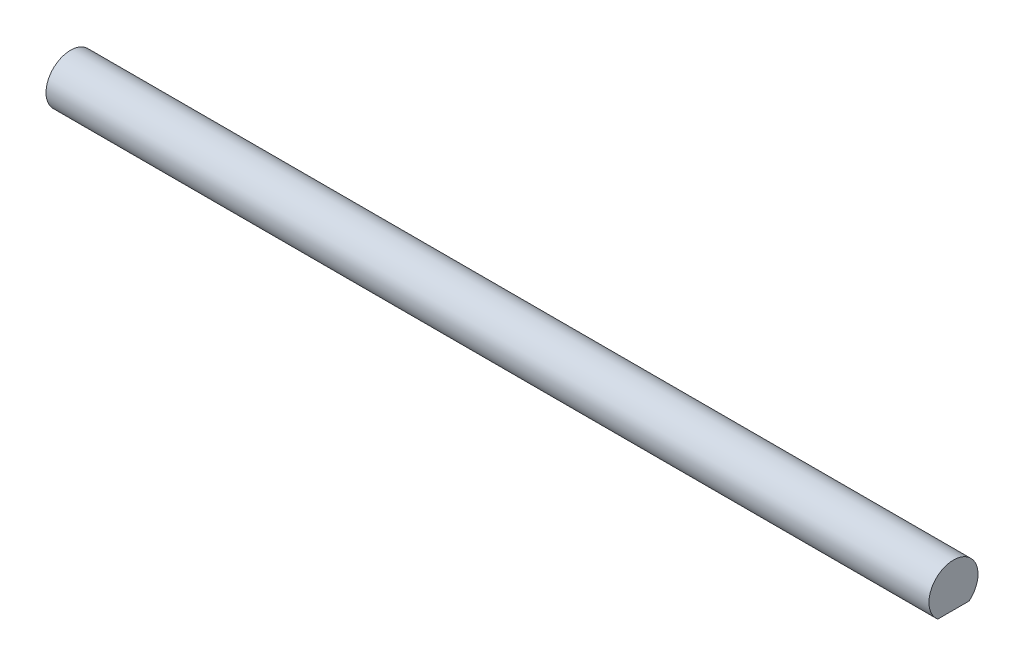
SolidWorks part; units mm, degrees
ref_plane "Front Plane" through (0, 0, 0) normal (0, 0, 1) x (1, 0, 0)
ref_plane "Top Plane" through (0, 0, 0) normal (0, 1, 0) x (1, 0, 0)
ref_plane "Right Plane" through (0, 0, 0) normal (1, 0, 0) x (0, 0, -1)
sketch "Sketch1" plane through (0, 0, 0) normal (1, 0, 0) x (0, 0, -1)
  line L0 (-2.032, -2.4396) -> (2.032, -2.4396)
  circle A0 centre (0, 0) radius 3.175
  dimension "D1" = 6.35
  dimension "D2" = 4.064
extrude "Boss-Extrude1" add sketch "Sketch1" along normal blind 304.8 contours L0 A0
sketch "Sketch2" plane through (304.8, 0, 0) normal (1, 0, 0) x (0, 0, -1)
  circle A0 centre (0, 0) radius 3.175
extrude "Cut-Extrude1" cut sketch "Sketch2" against normal blind 190.5
sketch "Sketch3" [suppressed] plane through (304.8, 0, 0) normal (1, 0, 0) x (0, 0, -1)
  circle A0 centre (0, 0) radius 3.175
extrude "Cut-Extrude2" [suppressed] cut sketch "Sketch3" against normal blind 228.6
sketch "Sketch4" [suppressed] plane through (304.8, 0, 0) normal (1, 0, 0) x (0, 0, -1)
  circle A0 centre (0, 0) radius 3.175
  dimension "D1" = 6.35
extrude "Cut-Extrude3" [suppressed] cut sketch "Sketch4" against normal blind 179.07
